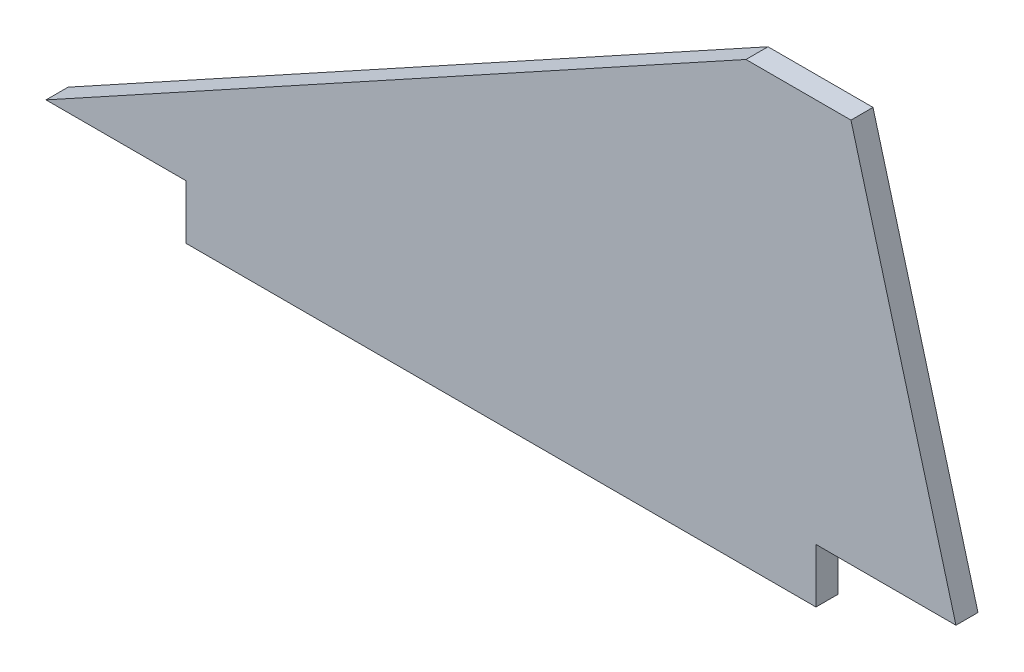
SolidWorks part; units mm, degrees
material "A-Glass Fiber"
ref_plane "Front Plane" through (0, 0, 0) normal (0, 0, 1) x (1, 0, 0)
ref_plane "Top Plane" through (0, 0, 0) normal (0, 1, 0) x (1, 0, 0)
ref_plane "Right Plane" through (0, 0, 0) normal (1, 0, 0) x (0, 0, -1)
sketch "Sketch1" plane through (0, 0, 0) normal (0, 0, 1) x (1, 0, 0)
  line L0 (0, 0) -> (20, 0)
  line L1 (20, 0) -> (20, -7.747)
  line L2 (20, -7.747) -> (110, -7.747)
  line L3 (110, -7.747) -> (110, 0)
  line L4 (110, 0) -> (130, 0)
  line L5 (130, 0) -> (115, 55)
  line L6 (115, 55) -> (100, 55)
  line L7 (100, 55) -> (0, 0)
  dimension "D1" = 20
  dimension "D2" = 7.747
  dimension "D3" = 90
  dimension "D4" = 20
  dimension "D5" = 15
  dimension "D6" = 15
  dimension "D7" = 55
extrude "Boss-Extrude1" add sketch "Sketch1" along normal blind 3.1496
